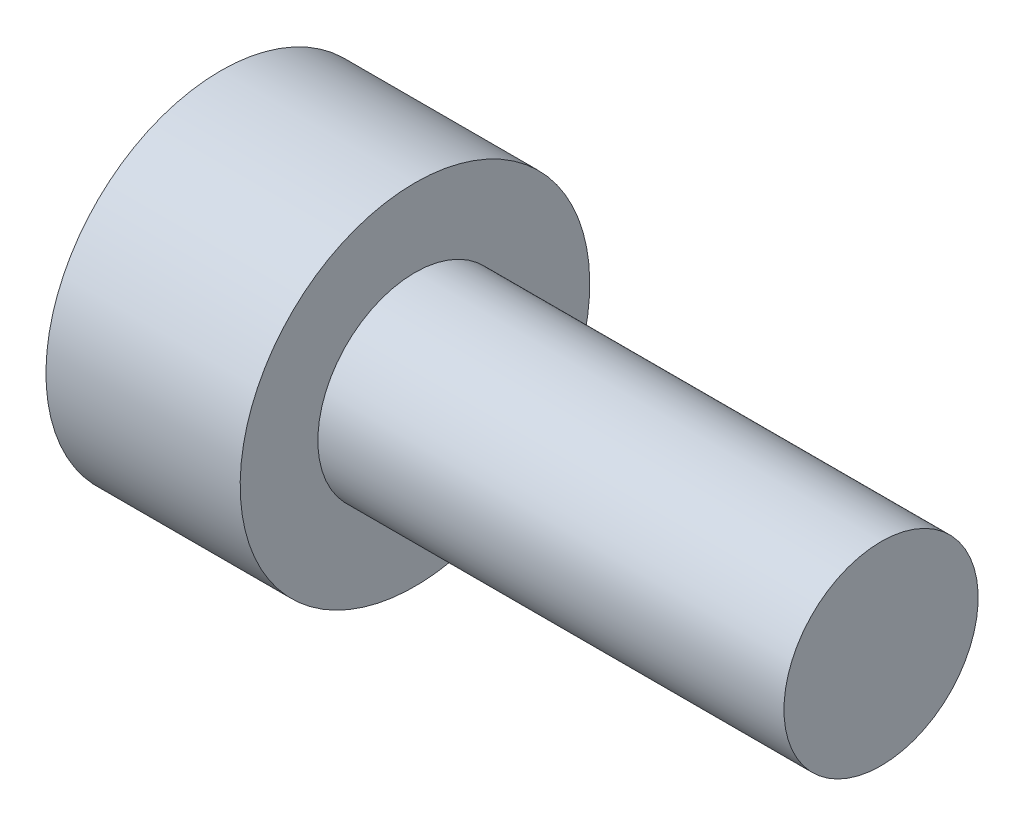
SolidWorks part; units mm, degrees
material "AISI Type 316L stainless steel"
ref_plane "Front Plane" through (0, 0, 0) normal (0, 0, 1) x (1, 0, 0)
ref_plane "Top Plane" through (0, 0, 0) normal (0, 1, 0) x (1, 0, 0)
ref_plane "Right Plane" through (0, 0, 0) normal (1, 0, 0) x (0, 0, -1)
sketch "Sketch1" plane through (0, 0, 0) normal (0, 0, 1) x (1, 0, 0)
  line L0 (0, 0) -> (0, 2.25)
  line L1 (0, 2.25) -> (2.5, 2.25)
  line L2 (2.5, 2.25) -> (2.5, 1.25)
  line L3 (2.5, 1.25) -> (8.5, 1.25)
  line L4 (8.5, 1.25) -> (8.5, 0)
  line L5 (8.5, 0) -> (0, 0)
  dimension "D1" = 2.25
  dimension "D2" = 2.5
  dimension "D3" = 1.25
  dimension "D4" = 6
revolve "Revolve1" add sketch "Sketch1" angle 360 about L5
sketch "Sketch2" plane through (0, 0, 0) normal (-1, 0, 0) x (0, 0, 1)
  line L1 (1.1547, 0) -> (0.5774, 1)
  line L2 (0.5774, 1) -> (-0.5774, 1)
  line L3 (-0.5774, 1) -> (-1.1547, 0)
  line L4 (-1.1547, 0) -> (-0.5774, -1)
  line L5 (-0.5774, -1) -> (0.5774, -1)
  line L6 (0.5774, -1) -> (1.1547, 0)
  circle A0 centre (0, 0) radius 1 construction
  dimension "D1" = 2
extrude "Cut-Extrude1" cut sketch "Sketch2" against normal blind 1.5
